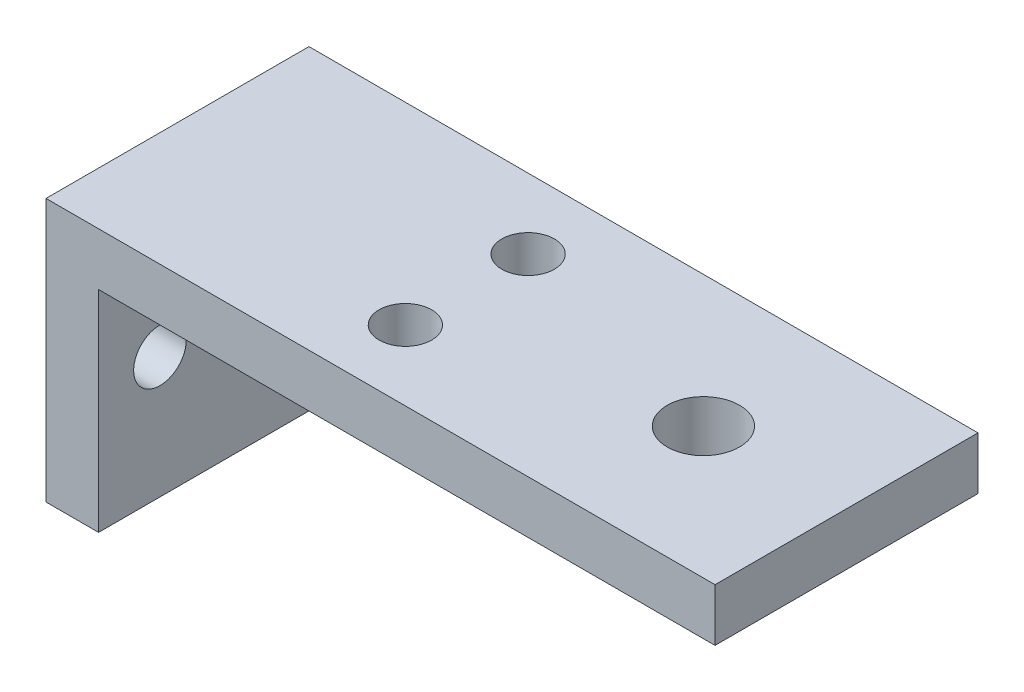
SolidWorks part; units mm, degrees
ref_plane "Front Plane" through (0, 0, 0) normal (0, 0, 1) x (1, 0, 0)
ref_plane "Top Plane" through (0, 0, 0) normal (0, 1, 0) x (1, 0, 0)
ref_plane "Right Plane" through (0, 0, 0) normal (1, 0, 0) x (0, 0, -1)
sketch "Croquis1" plane through (0, 0, 0) normal (0, 0, 1) x (1, 0, 0)
  line L1 (-1.5, 7.5) -> (1.5, 7.5)
  line L2 (-1.5, 7.5) -> (-1.5, -7.5)
  line L3 (-1.5, -7.5) -> (1.5, -7.5)
  line L4 (1.5, 7.5) -> (1.5, -7.5)
  line L5 (-1.5, 7.5) -> (1.5, -7.5) construction
  line L6 (-1.5, -7.5) -> (1.5, 7.5) construction
  line L7 (-1.5, 7.5) -> (48.5, 7.5)
  line L8 (-1.5, 7.5) -> (-1.5, 4.5)
  line L9 (-1.5, 4.5) -> (48.5, 4.5)
  line L10 (48.5, 7.5) -> (48.5, 4.5)
  line L11 (-1.5, 7.5) -> (48.5, 4.5) construction
  line L12 (-1.5, 4.5) -> (48.5, 7.5) construction
  point P0 (0, 0)
  point P5 (23.5, 6)
  dimension "D1" = 3
  dimension "D2" = 15
  dimension "D3" = 3
  dimension "D4" = 50
extrude "Saliente-Extruir1" add sketch "Croquis1" along normal blind 15 contours L9 L2 L3 L4 | L2 L9 L4 L1 | L10 L7 L4 L9
sketch "Croquis2" plane through (1.5, 0, 0) normal (1, 0, 0) x (0, 0, -1)
  line L2 (-15, 7.5) -> (-15, -7.5) construction
  line L3 (-15, 7.5) -> (0, 7.5) construction
  circle A5 centre (-11.5, -0.5) radius 1.5
  circle A6 centre (-4, -0.5) radius 1.5
  dimension "D1" = 3
  dimension "D4" = 3.5
  dimension "D6" = 8
  dimension "D2" = 3
  dimension "D3" = 7.5
  dimension "D5" = 8
extrude "Cortar-Extruir1" cut sketch "Croquis2" against normal blind 30
sketch "Croquis4" plane through (0, 7.5, 0) normal (0, 1, 0) x (1, 0, 0)
  line L0 (-1.5, -15) -> (-1.5, 0) construction
  circle A0 centre (28.5, -7.5) radius 2.0637
  dimension "D1" = 30
extrude "Cortar-Extruir3" cut sketch "Croquis4" against normal blind 10
sketch "Croquis5" plane through (0, 7.5, 0) normal (0, 1, 0) x (1, 0, 0)
  line L0 (48.5, -15) -> (36.6642, -15)
  line L1 (-1.5, -15) -> (48.5, -15) construction
  line L2 (36.6642, -15) -> (36.6642, 0)
  line L3 (-1.5, 0) -> (48.5, 0) construction
  line L4 (36.6642, 0) -> (48.5, 0)
  line L5 (48.5, 0) -> (48.5, -15)
extrude "Cortar-Extruir4" cut sketch "Croquis5" against normal blind 30
sketch "Croquis6" plane through (0, 7.5, 0) normal (0, 1, 0) x (1, 0, 0)
  line L0 (0, 0) -> (-1.5, 0) construction
  line L1 (0, 0) -> (15, 0) construction
  line L2 (-1.5, 0) -> (36.6642, 0) construction
  line L3 (15, 0) -> (15, -15) construction
  line L4 (-1.5, -15) -> (36.6642, -15) construction
  circle A1 centre (15, -4) radius 1.5
  circle A2 centre (15, -11) radius 1.5
  dimension "D2" = 3
  dimension "D3" = 3
  dimension "D1" = 15
  dimension "D4" = 4
  dimension "D5" = 4
extrude "Cortar-Extruir5" cut sketch "Croquis6" against normal blind 10
